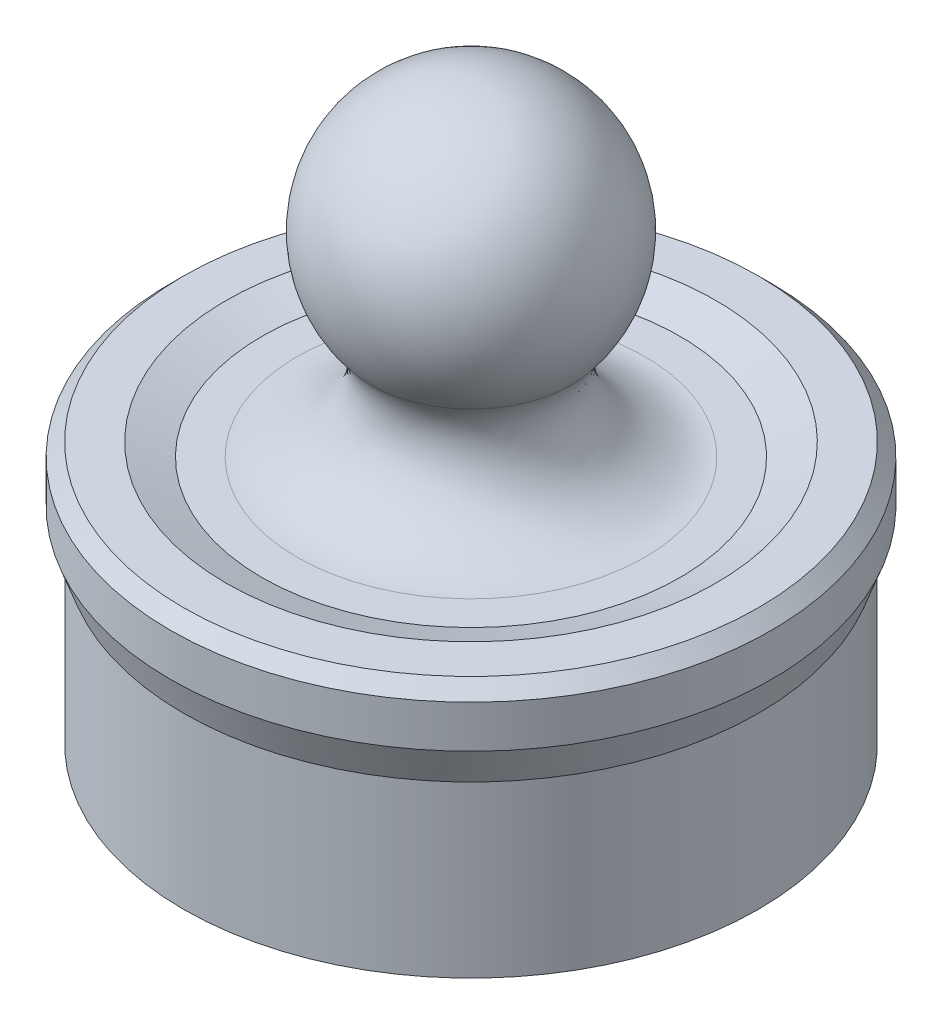
SolidWorks part; units mm, degrees
ref_plane "Front Plane" through (0, 0, 0) normal (0, 0, 1) x (1, 0, 0)
ref_plane "Top Plane" through (0, 0, 0) normal (0, 1, 0) x (1, 0, 0)
ref_plane "Right Plane" through (0, 0, 0) normal (1, 0, 0) x (0, 0, -1)
sketch "Sketch1" plane through (0, 0, 0) normal (0, 0, 1) x (1, 0, 0)
  line L0 (-9, -7.5) -> (-9, 0)
  line L1 (-9, 0) -> (0, 0)
  line L4 (0, 0) -> (0, 2)
  line L5 (-9, -7.5) -> (-11, -7.5)
  line L6 (-11, -7.5) -> (-11, -1)
  line L8 (-8, 2) -> (-6.6553, 2)
  line L9 (-8, 2) -> (-9.3737, 2.5)
  line L10 (-9.3737, 2.5) -> (-11, 2.5)
  line L12 (-11, 2) -> (-11.75, 2.75) construction
  line L13 (-11, -1) -> (-11.5, 0.3737)
  line L14 (-11.5, 0.3737) -> (-11.5, 2)
  line L15 (-11.5, 2) -> (-11, 2.5)
  line L16 (-11, 2) -> (-8, 2) construction
  line L17 (-11, -1) -> (-11, 2) construction
  line L18 (0, 2) -> (0, 9.5) construction
  line L19 (-6.228, 2) -> (-7.0836, 2) construction
  line L20 (-3.845, 6.3038) -> (-4.3336, 6.8915) construction
  line L21 (-4.4252, 7.0017) -> (-3.0049, 5.2931) construction
  line L22 (0, 14.5) -> (0, 2)
  arc A2 (-3.845, 6.3038) -> (0, 14.5) centre (0, 9.5) cw
  spline S0 degree 3 poles (-6.6553, 2) (-6.1205, 2) (-5.2505, 2.3) (-3.5769, 3.3559) (-2.9574, 5.2359) (-3.845, 6.3038) knots 0 0 0 0 0.245004 0.484763 1 1 1 1
  dimension "D1" = 2
  dimension "D2" = 5
  dimension "D7" = 9
  dimension "D9" = 7.5
  dimension "D3" = 0.5
  dimension "D4" = 7.5
  dimension "D5" = 20
  dimension "D6" = 2
  dimension "D8" = 3
revolve "Revolve2" add sketch "Sketch1" angle 360 about L22
